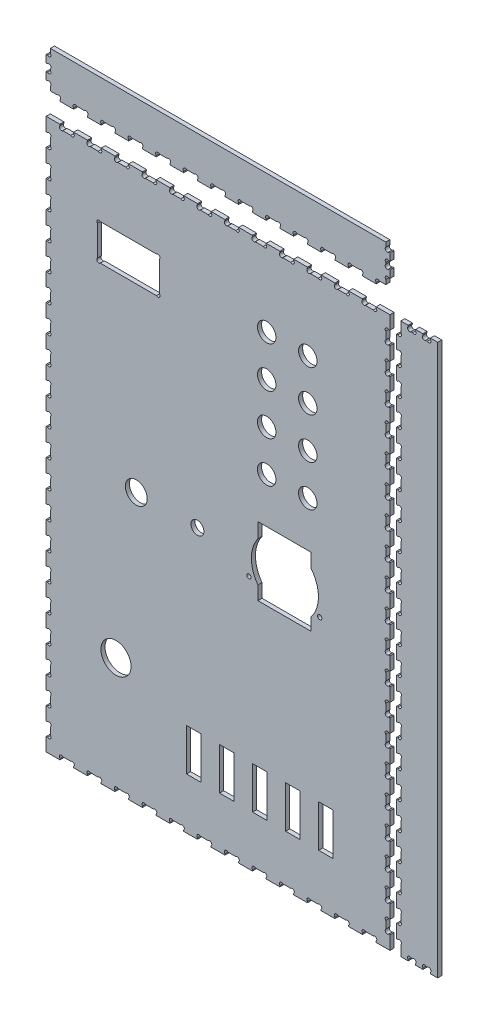
SolidWorks part; units mm, degrees
ref_plane "Alzado" through (0, 0, 0) normal (0, 0, 1) x (1, 0, 0)
ref_plane "Planta" through (0, 0, 0) normal (0, 1, 0) x (1, 0, 0)
ref_plane "Vista lateral" through (0, 0, 0) normal (1, 0, 0) x (0, 0, -1)
sketch "Croquis2" plane through (0, 0, 0) normal (0, 0, 1) x (1, 0, 0)
  line L0 (-12.45, -133) -> (1.075, -133) construction
  line L1 (-125.5, 201) -> (125.5, 201)
  line L2 (-125.5, 201) -> (-125.5, -201)
  line L3 (-125.5, -201) -> (125.5, -201)
  line L4 (125.5, 201) -> (125.5, -201)
  line L5 (-23.05, -163.7) -> (-12.45, -163.7)
  line L6 (-23.05, -163.7) -> (-23.05, -133)
  line L7 (-23.05, -133) -> (-12.45, -133)
  line L8 (-12.45, -163.7) -> (-12.45, -133)
  line L9 (1.075, -163.7) -> (11.675, -163.7)
  line L10 (1.075, -163.7) -> (1.075, -133)
  line L11 (1.075, -133) -> (11.675, -133)
  line L12 (11.675, -163.7) -> (11.675, -133)
  line L13 (25.2, -163.7) -> (35.8, -163.7)
  line L14 (25.2, -163.7) -> (25.2, -133)
  line L15 (25.2, -133) -> (35.8, -133)
  line L16 (35.8, -163.7) -> (35.8, -133)
  line L17 (49.325, -163.7) -> (59.925, -163.7)
  line L18 (49.325, -163.7) -> (49.325, -133)
  line L19 (49.325, -133) -> (59.925, -133)
  line L20 (59.925, -163.7) -> (59.925, -133)
  line L21 (73.45, -163.7) -> (84.05, -163.7)
  line L22 (73.45, -163.7) -> (73.45, -133)
  line L23 (73.45, -133) -> (84.05, -133)
  line L24 (84.05, -163.7) -> (84.05, -133)
  line L25 (11.675, -133) -> (25.2, -133) construction
  line L26 (35.8, -133) -> (49.325, -133) construction
  line L27 (59.925, -133) -> (73.45, -133) construction
  line L28 (22.55, -15.8999) -> (74.25, -15.8999) construction
  line L29 (29.1, 22) -> (67.7, 22)
  line L30 (29.1, 22) -> (29.1, 11.0846)
  line L31 (29.1, -28) -> (67.7, -28)
  line L32 (67.7, 22) -> (67.7, 12.0728)
  line L33 (48.4, -15.8999) -> (48.4, -28) construction
  line L34 (-125.5, -201) -> (125.5, 201) construction
  line L35 (-86.0286, 154.1488) -> (-44.9712, 154.1488)
  line L36 (-42.8499, 152.0275) -> (-42.8499, 129.9701)
  line L37 (-44.9712, 127.8488) -> (-86.0286, 127.8488)
  line L38 (-88.1499, 129.9701) -> (-88.1499, 152.0275)
  line L39 (29.1, 22) -> (67.7, -28) construction
  line L40 (-87.0892, 153.0881) -> (-43.9106, 153.0881) construction
  line L41 (-87.0892, 153.0881) -> (-87.0892, 128.9095) construction
  line L42 (-87.0892, 128.9095) -> (-43.9106, 128.9095) construction
  line L43 (-44.3499, 152.6488) -> (-42.8499, 154.1488) construction
  line L44 (-44.3499, 129.3488) -> (-42.8499, 127.8488) construction
  line L45 (-65.4999, 160.8921) -> (-65.4999, 137.3303) construction
  line L46 (-43.9106, 153.0881) -> (-43.9106, 128.9095) construction
  line L47 (29.1, -18.0846) -> (29.1, -28)
  line L48 (67.7, -19.0728) -> (67.7, -28)
  circle A0 centre (-74.55, -116) radius 11
  circle A1 centre (22.55, -15.8999) radius 1.55
  circle A2 centre (74.25, -15.8999) radius 1.55
  circle A3 centre (-15.0999, -4) radius 4.75
  circle A4 centre (-59.72, -4) radius 8
  arc A5 (-42.8499, 152.0275) -> (-44.9712, 154.1488) centre (-43.9106, 153.0881) ccw
  circle A6 centre (-44.3499, 152.6488) radius 1.5 construction
  arc A7 (-44.9712, 127.8488) -> (-42.8499, 129.9701) centre (-43.9106, 128.9095) ccw
  circle A8 centre (-44.3499, 129.3488) radius 1.5 construction
  arc A9 (-86.0286, 127.8488) -> (-88.1499, 129.9701) centre (-87.0892, 128.9095) cw
  arc A10 (-88.1499, 152.0275) -> (-86.0286, 154.1488) centre (-87.0892, 153.0881) cw
  circle A11 centre (65.5, 145) radius 6.75
  circle A12 centre (35.5, 145) radius 6.75
  circle A13 centre (35.5, 115) radius 6.75
  circle A14 centre (65.5, 115) radius 6.75
  circle A15 centre (35.5, 85) radius 6.75
  circle A16 centre (65.5, 85) radius 6.75
  circle A17 centre (35.5, 55) radius 6.75
  circle A18 centre (65.5, 55) radius 6.75
  arc A19 (29.1, 11.0846) -> (29.1, -18.0846) centre (48.786, -3.5) ccw
  arc A20 (67.7, -19.0728) -> (67.7, 12.0728) centre (48.786, -3.5) ccw
  dimension "D1" = 22
  dimension "D11" = 3.1
  dimension "D18" = 9.5
  dimension "D19" = 16
  dimension "D20" = 65.78
  dimension "D25" = 3
  dimension "D26" = 3
  dimension "D27" = 22.65
  dimension "D21" = 13.5
  dimension "D28" = 60
  dimension "D29" = 56
  dimension "D32" = 205
  dimension "D33" = 110.4001
  dimension "D37" = 49
  dimension "D2" = 402
  dimension "D3" = 251
  dimension "D4" = 10.6
  dimension "D5" = 30.7
  dimension "D6" = 13.525
  dimension "D7" = 41.45
  dimension "D8" = 37.3
  dimension "D9" = 38.6
  dimension "D10" = 50
  dimension "D12" = 51.7
  dimension "D13" = 12.1001
  dimension "D14" = 57.8
  dimension "D15" = 173
  dimension "D16" = 50.95
  dimension "D17" = 85
  dimension "D22" = 30
  dimension "D23" = 37.3501
  dimension "D24" = 46.8512
  dimension "D31" = 30
  dimension "D34" = 26.3
  dimension "D35" = 24.1787
  dimension "D36" = 43.1787
  dimension "D30" = 4
extrude "Saliente-Extruir2" add sketch "Croquis2" along normal blind 3 separate body
sketch "Croquis4" plane through (0, 0, 3) normal (0, 0, 1) x (1, 0, 0)
  line L0 (-125.5, 191.1951) -> (-122.45, 191.1951)
  line L1 (-125.5, 201) -> (-125.5, -201) construction
  line L2 (-122.45, 191.1951) -> (-122.45, 181.3902)
  line L3 (-122.45, 181.3902) -> (-125.5, 181.3902)
  line L4 (-125.5, 191.1951) -> (-125.5, 181.3902)
  line L5 (-125.5, 201) -> (-125.5, 191.1951) construction
  line L6 (-125.5, 181.3902) -> (-125.5, 171.5854) construction
  line L7 (-125.5, 171.5854) -> (-122.45, 171.5854)
  line L8 (-122.45, 171.5854) -> (-122.45, 161.7805)
  line L9 (-122.45, 161.7805) -> (-125.5, 161.7805)
  line L10 (-125.5, 171.5854) -> (-125.5, 161.7805)
  line L11 (-125.5, 161.7805) -> (-125.5, 151.9756) construction
  line L12 (-125.5, 151.9756) -> (-122.45, 151.9756)
  line L13 (-122.45, 151.9756) -> (-122.45, 142.1707)
  line L14 (-122.45, 142.1707) -> (-125.5, 142.1707)
  line L15 (-125.5, 151.9756) -> (-125.5, 142.1707)
  line L16 (-125.5, 142.1707) -> (-125.5, 132.3659) construction
  line L17 (-125.5, 132.3659) -> (-122.45, 132.3659)
  line L18 (-122.45, 132.3659) -> (-122.45, 122.561)
  line L19 (-122.45, 122.561) -> (-125.5, 122.561)
  line L20 (-125.5, 132.3659) -> (-125.5, 122.561)
  line L21 (-125.5, 122.561) -> (-125.5, 112.7561) construction
  line L22 (-125.5, 112.7561) -> (-122.45, 112.7561)
  line L23 (-122.45, 112.7561) -> (-122.45, 102.9512)
  line L24 (-122.45, 102.9512) -> (-125.5, 102.9512)
  line L25 (-125.5, 112.7561) -> (-125.5, 102.9512)
  line L26 (-125.5, 102.9512) -> (-125.5, 93.1463) construction
  line L27 (-125.5, 93.1463) -> (-122.45, 93.1463)
  line L28 (-122.45, 93.1463) -> (-122.45, 83.3415)
  line L29 (-122.45, 83.3415) -> (-125.5, 83.3415)
  line L30 (-125.5, 93.1463) -> (-125.5, 83.3415)
  line L31 (-125.5, 83.3415) -> (-125.5, 73.5366) construction
  line L32 (-125.5, 73.5366) -> (-122.45, 73.5366)
  line L33 (-122.45, 73.5366) -> (-122.45, 63.7317)
  line L34 (-122.45, 63.7317) -> (-125.5, 63.7317)
  line L35 (-125.5, 73.5366) -> (-125.5, 63.7317)
  line L36 (-125.5, 63.7317) -> (-125.5, 53.9268) construction
  line L37 (-125.5, 53.9268) -> (-122.45, 53.9268)
  line L38 (-122.45, 53.9268) -> (-122.45, 44.122)
  line L39 (-122.45, 44.122) -> (-125.5, 44.122)
  line L40 (-125.5, 53.9268) -> (-125.5, 44.122)
  line L41 (-125.5, 44.122) -> (-125.5, 34.3171) construction
  line L42 (-125.5, 34.3171) -> (-122.45, 34.3171)
  line L43 (-122.45, 34.3171) -> (-122.45, 24.5122)
  line L44 (-122.45, 24.5122) -> (-125.5, 24.5122)
  line L45 (-125.5, 34.3171) -> (-125.5, 24.5122)
  line L46 (-125.5, 24.5122) -> (-125.5, 14.7073) construction
  line L47 (-125.5, 14.7073) -> (-122.45, 14.7073)
  line L48 (-122.45, 14.7073) -> (-122.45, 4.9024)
  line L49 (-122.45, 4.9024) -> (-125.5, 4.9024)
  line L50 (-125.5, 14.7073) -> (-125.5, 4.9024)
  line L51 (-125.5, 4.9024) -> (-125.5, -4.9024) construction
  line L52 (-125.5, -4.9024) -> (-122.45, -4.9024)
  line L53 (-122.45, -4.9024) -> (-122.45, -14.7073)
  line L54 (-122.45, -14.7073) -> (-125.5, -14.7073)
  line L55 (-125.5, -4.9024) -> (-125.5, -14.7073)
  line L56 (-125.5, -14.7073) -> (-125.5, -24.5122) construction
  line L57 (-125.5, -24.5122) -> (-122.45, -24.5122)
  line L58 (-122.45, -24.5122) -> (-122.45, -34.3171)
  line L59 (-122.45, -34.3171) -> (-125.5, -34.3171)
  line L60 (-125.5, -24.5122) -> (-125.5, -34.3171)
  line L61 (-125.5, -34.3171) -> (-125.5, -44.122) construction
  line L62 (-125.5, -44.122) -> (-122.45, -44.122)
  line L63 (-122.45, -44.122) -> (-122.45, -53.9268)
  line L64 (-122.45, -53.9268) -> (-125.5, -53.9268)
  line L65 (-125.5, -44.122) -> (-125.5, -53.9268)
  line L66 (-125.5, -53.9268) -> (-125.5, -63.7317) construction
  line L67 (-125.5, -63.7317) -> (-122.45, -63.7317)
  line L68 (-122.45, -63.7317) -> (-122.45, -73.5366)
  line L69 (-122.45, -73.5366) -> (-125.5, -73.5366)
  line L70 (-125.5, -63.7317) -> (-125.5, -73.5366)
  line L71 (-125.5, -73.5366) -> (-125.5, -83.3415) construction
  line L72 (-125.5, -83.3415) -> (-122.45, -83.3415)
  line L73 (-122.45, -83.3415) -> (-122.45, -93.1463)
  line L74 (-122.45, -93.1463) -> (-125.5, -93.1463)
  line L75 (-125.5, -83.3415) -> (-125.5, -93.1463)
  line L76 (-125.5, -93.1463) -> (-125.5, -102.9512) construction
  line L77 (-125.5, -102.9512) -> (-122.45, -102.9512)
  line L78 (-122.45, -102.9512) -> (-122.45, -112.7561)
  line L79 (-122.45, -112.7561) -> (-125.5, -112.7561)
  line L80 (-125.5, -102.9512) -> (-125.5, -112.7561)
  line L81 (-125.5, -112.7561) -> (-125.5, -122.561) construction
  line L82 (-125.5, -122.561) -> (-122.45, -122.561)
  line L83 (-122.45, -122.561) -> (-122.45, -132.3659)
  line L84 (-122.45, -132.3659) -> (-125.5, -132.3659)
  line L85 (-125.5, -122.561) -> (-125.5, -132.3659)
  line L86 (-125.5, -132.3659) -> (-125.5, -142.1707) construction
  line L87 (-125.5, -142.1707) -> (-122.45, -142.1707)
  line L88 (-122.45, -142.1707) -> (-122.45, -151.9756)
  line L89 (-122.45, -151.9756) -> (-125.5, -151.9756)
  line L90 (-125.5, -142.1707) -> (-125.5, -151.9756)
  line L91 (-125.5, -151.9756) -> (-125.5, -161.7805) construction
  line L92 (-125.5, -161.7805) -> (-122.45, -161.7805)
  line L93 (-122.45, -161.7805) -> (-122.45, -171.5854)
  line L94 (-122.45, -171.5854) -> (-125.5, -171.5854)
  line L95 (-125.5, -161.7805) -> (-125.5, -171.5854)
  line L96 (-125.5, -171.5854) -> (-125.5, -181.3902) construction
  line L97 (-125.5, -181.3902) -> (-122.45, -181.3902)
  line L98 (-122.45, -181.3902) -> (-122.45, -191.1951)
  line L99 (-122.45, -191.1951) -> (-125.5, -191.1951)
  line L100 (-125.5, -181.3902) -> (-125.5, -191.1951)
  line L101 (-125.5, -191.1951) -> (-125.5, -201) construction
  line L102 (0, 201) -> (0, 0) construction
  line L103 (125.5, 201) -> (-125.5, 201) construction
  line L104 (125.5, -191.1951) -> (125.5, -201) construction
  line L105 (125.5, -171.5854) -> (125.5, -181.3902) construction
  line L106 (125.5, -151.9756) -> (125.5, -161.7805) construction
  line L107 (125.5, -132.3659) -> (125.5, -142.1707) construction
  line L108 (125.5, -112.7561) -> (125.5, -122.561) construction
  line L109 (125.5, -93.1463) -> (125.5, -102.9512) construction
  line L110 (125.5, -73.5366) -> (125.5, -83.3415) construction
  line L111 (125.5, -53.9268) -> (125.5, -63.7317) construction
  line L112 (125.5, -34.3171) -> (125.5, -44.122) construction
  line L113 (125.5, -14.7073) -> (125.5, -24.5122) construction
  line L114 (125.5, 4.9024) -> (125.5, -4.9024) construction
  line L115 (125.5, 24.5122) -> (125.5, 14.7073) construction
  line L116 (125.5, 44.122) -> (125.5, 34.3171) construction
  line L117 (125.5, 63.7317) -> (125.5, 53.9268) construction
  line L118 (125.5, 83.3415) -> (125.5, 73.5366) construction
  line L119 (125.5, 102.9512) -> (125.5, 93.1463) construction
  line L120 (125.5, 122.561) -> (125.5, 112.7561) construction
  line L121 (125.5, 142.1707) -> (125.5, 132.3659) construction
  line L122 (125.5, 161.7805) -> (125.5, 151.9756) construction
  line L123 (125.5, 181.3902) -> (125.5, 171.5854) construction
  line L124 (125.5, 201) -> (125.5, 191.1951) construction
  line L125 (125.5, -181.3902) -> (125.5, -191.1951)
  line L126 (122.45, -191.1951) -> (125.5, -191.1951)
  line L127 (122.45, -181.3902) -> (122.45, -191.1951)
  line L128 (125.5, -181.3902) -> (122.45, -181.3902)
  line L129 (125.5, -161.7805) -> (125.5, -171.5854)
  line L130 (122.45, -171.5854) -> (125.5, -171.5854)
  line L131 (122.45, -161.7805) -> (122.45, -171.5854)
  line L132 (125.5, -161.7805) -> (122.45, -161.7805)
  line L133 (125.5, -142.1707) -> (125.5, -151.9756)
  line L134 (122.45, -151.9756) -> (125.5, -151.9756)
  line L135 (122.45, -142.1707) -> (122.45, -151.9756)
  line L136 (125.5, -142.1707) -> (122.45, -142.1707)
  line L137 (125.5, -122.561) -> (125.5, -132.3659)
  line L138 (122.45, -132.3659) -> (125.5, -132.3659)
  line L139 (122.45, -122.561) -> (122.45, -132.3659)
  line L140 (125.5, -122.561) -> (122.45, -122.561)
  line L141 (125.5, -102.9512) -> (125.5, -112.7561)
  line L142 (122.45, -112.7561) -> (125.5, -112.7561)
  line L143 (122.45, -102.9512) -> (122.45, -112.7561)
  line L144 (125.5, -102.9512) -> (122.45, -102.9512)
  line L145 (125.5, -83.3415) -> (125.5, -93.1463)
  line L146 (122.45, -93.1463) -> (125.5, -93.1463)
  line L147 (122.45, -83.3415) -> (122.45, -93.1463)
  line L148 (125.5, -83.3415) -> (122.45, -83.3415)
  line L149 (125.5, -63.7317) -> (125.5, -73.5366)
  line L150 (122.45, -73.5366) -> (125.5, -73.5366)
  line L151 (122.45, -63.7317) -> (122.45, -73.5366)
  line L152 (125.5, -63.7317) -> (122.45, -63.7317)
  line L153 (125.5, -44.122) -> (125.5, -53.9268)
  line L154 (122.45, -53.9268) -> (125.5, -53.9268)
  line L155 (122.45, -44.122) -> (122.45, -53.9268)
  line L156 (125.5, -44.122) -> (122.45, -44.122)
  line L157 (125.5, -24.5122) -> (125.5, -34.3171)
  line L158 (122.45, -34.3171) -> (125.5, -34.3171)
  line L159 (122.45, -24.5122) -> (122.45, -34.3171)
  line L160 (125.5, -24.5122) -> (122.45, -24.5122)
  line L161 (125.5, -4.9024) -> (125.5, -14.7073)
  line L162 (122.45, -14.7073) -> (125.5, -14.7073)
  line L163 (122.45, -4.9024) -> (122.45, -14.7073)
  line L164 (125.5, -4.9024) -> (122.45, -4.9024)
  line L165 (125.5, 14.7073) -> (125.5, 4.9024)
  line L166 (122.45, 4.9024) -> (125.5, 4.9024)
  line L167 (122.45, 14.7073) -> (122.45, 4.9024)
  line L168 (125.5, 14.7073) -> (122.45, 14.7073)
  line L169 (125.5, 34.3171) -> (125.5, 24.5122)
  line L170 (122.45, 24.5122) -> (125.5, 24.5122)
  line L171 (122.45, 34.3171) -> (122.45, 24.5122)
  line L172 (125.5, 34.3171) -> (122.45, 34.3171)
  line L173 (125.5, 53.9268) -> (125.5, 44.122)
  line L174 (122.45, 44.122) -> (125.5, 44.122)
  line L175 (122.45, 53.9268) -> (122.45, 44.122)
  line L176 (125.5, 53.9268) -> (122.45, 53.9268)
  line L177 (125.5, 73.5366) -> (125.5, 63.7317)
  line L178 (122.45, 63.7317) -> (125.5, 63.7317)
  line L179 (122.45, 73.5366) -> (122.45, 63.7317)
  line L180 (125.5, 73.5366) -> (122.45, 73.5366)
  line L181 (125.5, 93.1463) -> (125.5, 83.3415)
  line L182 (122.45, 83.3415) -> (125.5, 83.3415)
  line L183 (122.45, 93.1463) -> (122.45, 83.3415)
  line L184 (125.5, 93.1463) -> (122.45, 93.1463)
  line L185 (125.5, 112.7561) -> (125.5, 102.9512)
  line L186 (122.45, 102.9512) -> (125.5, 102.9512)
  line L187 (122.45, 112.7561) -> (122.45, 102.9512)
  line L188 (125.5, 112.7561) -> (122.45, 112.7561)
  line L189 (125.5, 132.3659) -> (125.5, 122.561)
  line L190 (122.45, 122.561) -> (125.5, 122.561)
  line L191 (122.45, 132.3659) -> (122.45, 122.561)
  line L192 (125.5, 132.3659) -> (122.45, 132.3659)
  line L193 (125.5, 151.9756) -> (125.5, 142.1707)
  line L194 (122.45, 142.1707) -> (125.5, 142.1707)
  line L195 (122.45, 151.9756) -> (122.45, 142.1707)
  line L196 (125.5, 151.9756) -> (122.45, 151.9756)
  line L197 (125.5, 171.5854) -> (125.5, 161.7805)
  line L198 (122.45, 161.7805) -> (125.5, 161.7805)
  line L199 (122.45, 171.5854) -> (122.45, 161.7805)
  line L200 (125.5, 171.5854) -> (122.45, 171.5854)
  line L201 (125.5, 191.1951) -> (125.5, 181.3902)
  line L202 (122.45, 181.3902) -> (125.5, 181.3902)
  line L203 (122.45, 191.1951) -> (122.45, 181.3902)
  line L204 (125.5, 191.1951) -> (122.45, 191.1951)
  dimension "D1" = 3.05
  dimension "D2" = 20
extrude "Cortar-Extruir1" cut sketch "Croquis4" against normal through all
sketch "Croquis5" plane through (0, 0, 3) normal (0, 0, 1) x (1, 0, 0)
  line L0 (125.5, 201) -> (-125.5, 201) construction
  line L1 (-115.46, 201) -> (-105.42, 201)
  line L2 (-115.46, 201) -> (-115.46, 197.95)
  line L3 (-115.46, 197.95) -> (-105.42, 197.95)
  line L4 (-105.42, 201) -> (-105.42, 197.95)
  line L5 (-115.46, 201) -> (-125.5, 201) construction
  line L6 (-122.45, 191.1951) -> (-125.5, 191.1951) construction
  line L7 (-95.38, 201) -> (-85.34, 201)
  line L8 (-95.38, 201) -> (-95.38, 197.95)
  line L9 (-95.38, 197.95) -> (-85.34, 197.95)
  line L10 (-85.34, 201) -> (-85.34, 197.95)
  line L11 (-95.38, 201) -> (-105.42, 201) construction
  line L12 (-75.3, 201) -> (-65.26, 201)
  line L13 (-75.3, 201) -> (-75.3, 197.95)
  line L14 (-75.3, 197.95) -> (-65.26, 197.95)
  line L15 (-65.26, 201) -> (-65.26, 197.95)
  line L16 (-75.3, 201) -> (-85.34, 201) construction
  line L17 (-55.22, 201) -> (-45.18, 201)
  line L18 (-55.22, 201) -> (-55.22, 197.95)
  line L19 (-55.22, 197.95) -> (-45.18, 197.95)
  line L20 (-45.18, 201) -> (-45.18, 197.95)
  line L21 (-55.22, 201) -> (-65.26, 201) construction
  line L22 (-35.14, 201) -> (-25.1, 201)
  line L23 (-35.14, 201) -> (-35.14, 197.95)
  line L24 (-35.14, 197.95) -> (-25.1, 197.95)
  line L25 (-25.1, 201) -> (-25.1, 197.95)
  line L26 (-35.14, 201) -> (-45.18, 201) construction
  line L27 (-15.06, 201) -> (-5.02, 201)
  line L28 (-15.06, 201) -> (-15.06, 197.95)
  line L29 (-15.06, 197.95) -> (-5.02, 197.95)
  line L30 (-5.02, 201) -> (-5.02, 197.95)
  line L31 (-15.06, 201) -> (-25.1, 201) construction
  line L32 (5.02, 201) -> (15.06, 201)
  line L33 (5.02, 201) -> (5.02, 197.95)
  line L34 (5.02, 197.95) -> (15.06, 197.95)
  line L35 (15.06, 201) -> (15.06, 197.95)
  line L36 (5.02, 201) -> (-5.02, 201) construction
  line L37 (25.1, 201) -> (35.14, 201)
  line L38 (25.1, 201) -> (25.1, 197.95)
  line L39 (25.1, 197.95) -> (35.14, 197.95)
  line L40 (35.14, 201) -> (35.14, 197.95)
  line L41 (25.1, 201) -> (15.06, 201) construction
  line L42 (45.18, 201) -> (55.22, 201)
  line L43 (45.18, 201) -> (45.18, 197.95)
  line L44 (45.18, 197.95) -> (55.22, 197.95)
  line L45 (55.22, 201) -> (55.22, 197.95)
  line L46 (45.18, 201) -> (35.14, 201) construction
  line L47 (65.26, 201) -> (75.3, 201)
  line L48 (65.26, 201) -> (65.26, 197.95)
  line L49 (65.26, 197.95) -> (75.3, 197.95)
  line L50 (75.3, 201) -> (75.3, 197.95)
  line L51 (65.26, 201) -> (55.22, 201) construction
  line L52 (85.34, 201) -> (95.38, 201)
  line L53 (85.34, 201) -> (85.34, 197.95)
  line L54 (85.34, 197.95) -> (95.38, 197.95)
  line L55 (95.38, 201) -> (95.38, 197.95)
  line L56 (85.34, 201) -> (75.3, 201) construction
  line L57 (105.42, 201) -> (115.46, 201)
  line L58 (105.42, 201) -> (105.42, 197.95)
  line L59 (105.42, 197.95) -> (115.46, 197.95)
  line L60 (115.46, 201) -> (115.46, 197.95)
  line L61 (105.42, 201) -> (95.38, 201) construction
  line L62 (115.46, 201) -> (125.5, 201) construction
  line L63 (0, 0) -> (108.8157, 0) construction
  line L64 (115.46, -201) -> (125.5, -201) construction
  line L65 (105.42, -201) -> (95.38, -201) construction
  line L66 (85.34, -201) -> (75.3, -201) construction
  line L67 (65.26, -201) -> (55.22, -201) construction
  line L68 (45.18, -201) -> (35.14, -201) construction
  line L69 (25.1, -201) -> (15.06, -201) construction
  line L70 (5.02, -201) -> (-5.02, -201) construction
  line L71 (-15.06, -201) -> (-25.1, -201) construction
  line L72 (-35.14, -201) -> (-45.18, -201) construction
  line L73 (-55.22, -201) -> (-65.26, -201) construction
  line L74 (-75.3, -201) -> (-85.34, -201) construction
  line L75 (-95.38, -201) -> (-105.42, -201) construction
  line L76 (-115.46, -201) -> (-125.5, -201) construction
  line L77 (115.46, -201) -> (115.46, -197.95)
  line L78 (105.42, -197.95) -> (115.46, -197.95)
  line L79 (105.42, -201) -> (105.42, -197.95)
  line L80 (105.42, -201) -> (115.46, -201)
  line L81 (95.38, -201) -> (95.38, -197.95)
  line L82 (85.34, -197.95) -> (95.38, -197.95)
  line L83 (85.34, -201) -> (85.34, -197.95)
  line L84 (85.34, -201) -> (95.38, -201)
  line L85 (75.3, -201) -> (75.3, -197.95)
  line L86 (65.26, -197.95) -> (75.3, -197.95)
  line L87 (65.26, -201) -> (65.26, -197.95)
  line L88 (65.26, -201) -> (75.3, -201)
  line L89 (55.22, -201) -> (55.22, -197.95)
  line L90 (45.18, -197.95) -> (55.22, -197.95)
  line L91 (45.18, -201) -> (45.18, -197.95)
  line L92 (45.18, -201) -> (55.22, -201)
  line L93 (35.14, -201) -> (35.14, -197.95)
  line L94 (25.1, -197.95) -> (35.14, -197.95)
  line L95 (25.1, -201) -> (25.1, -197.95)
  line L96 (25.1, -201) -> (35.14, -201)
  line L97 (15.06, -201) -> (15.06, -197.95)
  line L98 (5.02, -197.95) -> (15.06, -197.95)
  line L99 (5.02, -201) -> (5.02, -197.95)
  line L100 (5.02, -201) -> (15.06, -201)
  line L101 (-5.02, -201) -> (-5.02, -197.95)
  line L102 (-15.06, -197.95) -> (-5.02, -197.95)
  line L103 (-15.06, -201) -> (-15.06, -197.95)
  line L104 (-15.06, -201) -> (-5.02, -201)
  line L105 (-25.1, -201) -> (-25.1, -197.95)
  line L106 (-35.14, -197.95) -> (-25.1, -197.95)
  line L107 (-35.14, -201) -> (-35.14, -197.95)
  line L108 (-35.14, -201) -> (-25.1, -201)
  line L109 (-45.18, -201) -> (-45.18, -197.95)
  line L110 (-55.22, -197.95) -> (-45.18, -197.95)
  line L111 (-55.22, -201) -> (-55.22, -197.95)
  line L112 (-55.22, -201) -> (-45.18, -201)
  line L113 (-65.26, -201) -> (-65.26, -197.95)
  line L114 (-75.3, -197.95) -> (-65.26, -197.95)
  line L115 (-75.3, -201) -> (-75.3, -197.95)
  line L116 (-75.3, -201) -> (-65.26, -201)
  line L117 (-85.34, -201) -> (-85.34, -197.95)
  line L118 (-95.38, -197.95) -> (-85.34, -197.95)
  line L119 (-95.38, -201) -> (-95.38, -197.95)
  line L120 (-95.38, -201) -> (-85.34, -201)
  line L121 (-105.42, -201) -> (-105.42, -197.95)
  line L122 (-115.46, -197.95) -> (-105.42, -197.95)
  line L123 (-115.46, -201) -> (-115.46, -197.95)
  line L124 (-115.46, -201) -> (-105.42, -201)
  dimension "D1" = 12
extrude "Cortar-Extruir2" cut sketch "Croquis5" against normal through all
sketch "Croquis12" plane through (0, 0, 0) normal (0, 0, 1) x (1, 0, 0)
  line L1 (130.3668, 201) -> (160.3668, 201)
  line L2 (130.3668, 201) -> (130.3668, -201)
  line L3 (130.3668, -201) -> (160.3668, -201)
  line L4 (160.3668, 201) -> (160.3668, -201)
  line L5 (-125.5, 245.4596) -> (125.5, 245.4596)
  line L6 (-125.5, 245.4596) -> (-125.5, 215.4596)
  line L7 (-125.5, 215.4596) -> (125.5, 215.4596)
  line L8 (125.5, 245.4596) -> (125.5, 215.4596)
  line L13 (-125.5, 201) -> (-125.5, 191.1951) construction
  dimension "D1" = 402
  dimension "D2" = 30
  dimension "D3" = 251
extrude "Saliente-Extruir3" add sketch "Croquis12" along normal blind 3 separate body
sketch "Croquis13" plane through (0, 0, 3) normal (0, 0, 1) x (1, 0, 0)
  line L0 (130.3668, 201) -> (130.3668, -201) construction
  line L1 (130.3668, 201) -> (133.4168, 201)
  line L2 (130.3668, 201) -> (130.3668, 191.1951)
  line L3 (130.3668, 191.1951) -> (133.4168, 191.1951)
  line L4 (133.4168, 201) -> (133.4168, 191.1951)
  line L5 (160.3668, 201) -> (130.3668, 201) construction
  line L6 (125.5, 191.1951) -> (122.45, 191.1951) construction
  line L7 (130.3668, 191.1951) -> (130.3668, 181.3902) construction
  line L11 (130.3668, 181.3902) -> (133.4168, 181.3902)
  line L12 (130.3668, 181.3902) -> (130.3668, 171.5854)
  line L13 (130.3668, 171.5854) -> (133.4168, 171.5854)
  line L14 (133.4168, 181.3902) -> (133.4168, 171.5854)
  line L16 (130.3668, 161.7805) -> (133.4168, 161.7805)
  line L17 (130.3668, 161.7805) -> (130.3668, 151.9756)
  line L18 (130.3668, 151.9756) -> (133.4168, 151.9756)
  line L19 (133.4168, 161.7805) -> (133.4168, 151.9756)
  line L20 (130.3668, 171.5854) -> (130.3668, 161.7805) construction
  line L21 (130.3668, 142.1707) -> (133.4168, 142.1707)
  line L22 (130.3668, 142.1707) -> (130.3668, 132.3659)
  line L23 (130.3668, 132.3659) -> (133.4168, 132.3659)
  line L24 (133.4168, 142.1707) -> (133.4168, 132.3659)
  line L25 (130.3668, 151.9756) -> (130.3668, 142.1707) construction
  line L26 (130.3668, 122.561) -> (133.4168, 122.561)
  line L27 (130.3668, 122.561) -> (130.3668, 112.7561)
  line L28 (130.3668, 112.7561) -> (133.4168, 112.7561)
  line L29 (133.4168, 122.561) -> (133.4168, 112.7561)
  line L30 (130.3668, 132.3659) -> (130.3668, 122.561) construction
  line L31 (130.3668, 102.9512) -> (133.4168, 102.9512)
  line L32 (130.3668, 102.9512) -> (130.3668, 93.1463)
  line L33 (130.3668, 93.1463) -> (133.4168, 93.1463)
  line L34 (133.4168, 102.9512) -> (133.4168, 93.1463)
  line L35 (130.3668, 112.7561) -> (130.3668, 102.9512) construction
  line L36 (130.3668, 83.3415) -> (133.4168, 83.3415)
  line L37 (130.3668, 83.3415) -> (130.3668, 73.5366)
  line L38 (130.3668, 73.5366) -> (133.4168, 73.5366)
  line L39 (133.4168, 83.3415) -> (133.4168, 73.5366)
  line L40 (130.3668, 93.1463) -> (130.3668, 83.3415) construction
  line L41 (130.3668, 63.7317) -> (133.4168, 63.7317)
  line L42 (130.3668, 63.7317) -> (130.3668, 53.9268)
  line L43 (130.3668, 53.9268) -> (133.4168, 53.9268)
  line L44 (133.4168, 63.7317) -> (133.4168, 53.9268)
  line L45 (130.3668, 73.5366) -> (130.3668, 63.7317) construction
  line L46 (130.3668, 44.122) -> (133.4168, 44.122)
  line L47 (130.3668, 44.122) -> (130.3668, 34.3171)
  line L48 (130.3668, 34.3171) -> (133.4168, 34.3171)
  line L49 (133.4168, 44.122) -> (133.4168, 34.3171)
  line L50 (130.3668, 53.9268) -> (130.3668, 44.122) construction
  line L51 (130.3668, 24.5122) -> (133.4168, 24.5122)
  line L52 (130.3668, 24.5122) -> (130.3668, 14.7073)
  line L53 (130.3668, 14.7073) -> (133.4168, 14.7073)
  line L54 (133.4168, 24.5122) -> (133.4168, 14.7073)
  line L55 (130.3668, 34.3171) -> (130.3668, 24.5122) construction
  line L56 (130.3668, 4.9024) -> (133.4168, 4.9024)
  line L57 (130.3668, 4.9024) -> (130.3668, -4.9024)
  line L58 (130.3668, -4.9024) -> (133.4168, -4.9024)
  line L59 (133.4168, 4.9024) -> (133.4168, -4.9024)
  line L60 (130.3668, 14.7073) -> (130.3668, 4.9024) construction
  line L61 (130.3668, -14.7073) -> (133.4168, -14.7073)
  line L62 (130.3668, -14.7073) -> (130.3668, -24.5122)
  line L63 (130.3668, -24.5122) -> (133.4168, -24.5122)
  line L64 (133.4168, -14.7073) -> (133.4168, -24.5122)
  line L65 (130.3668, -4.9024) -> (130.3668, -14.7073) construction
  line L66 (130.3668, -34.3171) -> (133.4168, -34.3171)
  line L67 (130.3668, -34.3171) -> (130.3668, -44.122)
  line L68 (130.3668, -44.122) -> (133.4168, -44.122)
  line L69 (133.4168, -34.3171) -> (133.4168, -44.122)
  line L70 (130.3668, -24.5122) -> (130.3668, -34.3171) construction
  line L71 (130.3668, -53.9268) -> (133.4168, -53.9268)
  line L72 (130.3668, -53.9268) -> (130.3668, -63.7317)
  line L73 (130.3668, -63.7317) -> (133.4168, -63.7317)
  line L74 (133.4168, -53.9268) -> (133.4168, -63.7317)
  line L75 (130.3668, -44.122) -> (130.3668, -53.9268) construction
  line L76 (130.3668, -73.5366) -> (133.4168, -73.5366)
  line L77 (130.3668, -73.5366) -> (130.3668, -83.3415)
  line L78 (130.3668, -83.3415) -> (133.4168, -83.3415)
  line L79 (133.4168, -73.5366) -> (133.4168, -83.3415)
  line L80 (130.3668, -63.7317) -> (130.3668, -73.5366) construction
  line L81 (130.3668, -93.1463) -> (133.4168, -93.1463)
  line L82 (130.3668, -93.1463) -> (130.3668, -102.9512)
  line L83 (130.3668, -102.9512) -> (133.4168, -102.9512)
  line L84 (133.4168, -93.1463) -> (133.4168, -102.9512)
  line L85 (130.3668, -83.3415) -> (130.3668, -93.1463) construction
  line L86 (130.3668, -112.7561) -> (133.4168, -112.7561)
  line L87 (130.3668, -112.7561) -> (130.3668, -122.561)
  line L88 (130.3668, -122.561) -> (133.4168, -122.561)
  line L89 (133.4168, -112.7561) -> (133.4168, -122.561)
  line L90 (130.3668, -102.9512) -> (130.3668, -112.7561) construction
  line L91 (130.3668, -132.3659) -> (133.4168, -132.3659)
  line L92 (130.3668, -132.3659) -> (130.3668, -142.1707)
  line L93 (130.3668, -142.1707) -> (133.4168, -142.1707)
  line L94 (133.4168, -132.3659) -> (133.4168, -142.1707)
  line L95 (130.3668, -122.561) -> (130.3668, -132.3659) construction
  line L96 (130.3668, -151.9756) -> (133.4168, -151.9756)
  line L97 (130.3668, -151.9756) -> (130.3668, -161.7805)
  line L98 (130.3668, -161.7805) -> (133.4168, -161.7805)
  line L99 (133.4168, -151.9756) -> (133.4168, -161.7805)
  line L100 (130.3668, -142.1707) -> (130.3668, -151.9756) construction
  line L101 (130.3668, -171.5854) -> (133.4168, -171.5854)
  line L102 (130.3668, -171.5854) -> (130.3668, -181.3902)
  line L103 (130.3668, -181.3902) -> (133.4168, -181.3902)
  line L104 (133.4168, -171.5854) -> (133.4168, -181.3902)
  line L105 (130.3668, -161.7805) -> (130.3668, -171.5854) construction
  line L107 (130.3668, -201) -> (133.4168, -201)
  line L108 (130.3668, -201) -> (130.3668, -191.1951)
  line L109 (130.3668, -191.1951) -> (133.4168, -191.1951)
  line L110 (133.4168, -201) -> (133.4168, -191.1951)
  line L111 (122.45, 181.3902) -> (125.5, 181.3902) construction
  line L112 (125.5, 171.5854) -> (122.45, 171.5854) construction
  line L113 (122.45, -191.1951) -> (125.5, -191.1951) construction
  dimension "D4" = 19
extrude "Cortar-Extruir8" cut sketch "Croquis13" against normal through all
sketch "Croquis14" plane through (0, 0, 3) normal (0, 0, 1) x (1, 0, 0)
  line L0 (160.3668, 201) -> (133.4168, 201) construction
  line L1 (138.8068, 201) -> (144.1968, 201)
  line L2 (138.8068, 201) -> (138.8068, 197.95)
  line L3 (138.8068, 197.95) -> (144.1968, 197.95)
  line L4 (144.1968, 201) -> (144.1968, 197.95)
  line L5 (130.3668, 191.1951) -> (133.4168, 191.1951) construction
  line L6 (149.5868, 201) -> (154.9768, 201)
  line L7 (149.5868, 201) -> (149.5868, 197.95)
  line L8 (149.5868, 197.95) -> (154.9768, 197.95)
  line L9 (154.9768, 201) -> (154.9768, 197.95)
  line L10 (144.1968, 201) -> (149.5868, 201) construction
  line L11 (154.9768, 201) -> (160.3668, 201) construction
  line L12 (133.4168, 201) -> (138.8068, 201) construction
  line L13 (160.3668, 0) -> (144.1968, 0) construction
  line L14 (160.3668, -201) -> (160.3668, 201) construction
  line L15 (133.4168, -201) -> (138.8068, -201) construction
  line L16 (154.9768, -201) -> (160.3668, -201) construction
  line L17 (144.1968, -201) -> (149.5868, -201) construction
  line L18 (154.9768, -201) -> (154.9768, -197.95)
  line L19 (149.5868, -197.95) -> (154.9768, -197.95)
  line L20 (149.5868, -201) -> (149.5868, -197.95)
  line L21 (149.5868, -201) -> (154.9768, -201)
  line L22 (144.1968, -201) -> (144.1968, -197.95)
  line L23 (138.8068, -197.95) -> (144.1968, -197.95)
  line L24 (138.8068, -201) -> (138.8068, -197.95)
  line L25 (138.8068, -201) -> (144.1968, -201)
extrude "Cortar-Extruir9" cut sketch "Croquis14" against normal through all
sketch "Croquis16" plane through (0, 0, 3) normal (0, 0, 1) x (1, 0, 0)
  line L0 (-105.42, 197.95) -> (-105.42, 201) construction
  line L1 (-125.5, 215.4596) -> (125.5, 215.4596) construction
  line L2 (-125.5, 215.4596) -> (-115.46, 215.4596)
  line L3 (-125.5, 215.4596) -> (-125.5, 218.5096)
  line L4 (-125.5, 218.5096) -> (-115.46, 218.5096)
  line L5 (-115.46, 215.4596) -> (-115.46, 218.5096)
  line L6 (-95.38, 201) -> (-95.38, 197.95) construction
  line L10 (-115.46, 201) -> (-115.46, 197.95) construction
  line L12 (-125.5, 245.4596) -> (-125.5, 215.4596) construction
  line L13 (-115.46, 215.4596) -> (-105.42, 215.4596) construction
  line L14 (-105.42, 215.4596) -> (-95.38, 215.4596)
  line L15 (-105.42, 215.4596) -> (-105.42, 218.5096)
  line L16 (-105.42, 218.5096) -> (-95.38, 218.5096)
  line L17 (-95.38, 215.4596) -> (-95.38, 218.5096)
  line L20 (-85.34, 215.4596) -> (-75.3, 215.4596)
  line L21 (-85.34, 215.4596) -> (-85.34, 218.5096)
  line L22 (-85.34, 218.5096) -> (-75.3, 218.5096)
  line L23 (-75.3, 215.4596) -> (-75.3, 218.5096)
  line L24 (-95.38, 215.4596) -> (-85.34, 215.4596) construction
  line L25 (-65.26, 215.4596) -> (-55.22, 215.4596)
  line L26 (-65.26, 215.4596) -> (-65.26, 218.5096)
  line L27 (-65.26, 218.5096) -> (-55.22, 218.5096)
  line L28 (-55.22, 215.4596) -> (-55.22, 218.5096)
  line L29 (-75.3, 215.4596) -> (-65.26, 215.4596) construction
  line L30 (-45.18, 215.4596) -> (-35.14, 215.4596)
  line L31 (-45.18, 215.4596) -> (-45.18, 218.5096)
  line L32 (-45.18, 218.5096) -> (-35.14, 218.5096)
  line L33 (-35.14, 215.4596) -> (-35.14, 218.5096)
  line L34 (-55.22, 215.4596) -> (-45.18, 215.4596) construction
  line L35 (-25.1, 215.4596) -> (-15.06, 215.4596)
  line L36 (-25.1, 215.4596) -> (-25.1, 218.5096)
  line L37 (-25.1, 218.5096) -> (-15.06, 218.5096)
  line L38 (-15.06, 215.4596) -> (-15.06, 218.5096)
  line L39 (-35.14, 215.4596) -> (-25.1, 215.4596) construction
  line L40 (-5.02, 215.4596) -> (5.02, 215.4596)
  line L41 (-5.02, 215.4596) -> (-5.02, 218.5096)
  line L42 (-5.02, 218.5096) -> (5.02, 218.5096)
  line L43 (5.02, 215.4596) -> (5.02, 218.5096)
  line L44 (-15.06, 215.4596) -> (-5.02, 215.4596) construction
  line L45 (15.06, 215.4596) -> (25.1, 215.4596)
  line L46 (15.06, 215.4596) -> (15.06, 218.5096)
  line L47 (15.06, 218.5096) -> (25.1, 218.5096)
  line L48 (25.1, 215.4596) -> (25.1, 218.5096)
  line L49 (5.02, 215.4596) -> (15.06, 215.4596) construction
  line L50 (35.14, 215.4596) -> (45.18, 215.4596)
  line L51 (35.14, 215.4596) -> (35.14, 218.5096)
  line L52 (35.14, 218.5096) -> (45.18, 218.5096)
  line L53 (45.18, 215.4596) -> (45.18, 218.5096)
  line L54 (25.1, 215.4596) -> (35.14, 215.4596) construction
  line L55 (55.22, 215.4596) -> (65.26, 215.4596)
  line L56 (55.22, 215.4596) -> (55.22, 218.5096)
  line L57 (55.22, 218.5096) -> (65.26, 218.5096)
  line L58 (65.26, 215.4596) -> (65.26, 218.5096)
  line L59 (45.18, 215.4596) -> (55.22, 215.4596) construction
  line L60 (75.3, 215.4596) -> (85.34, 215.4596)
  line L61 (75.3, 215.4596) -> (75.3, 218.5096)
  line L62 (75.3, 218.5096) -> (85.34, 218.5096)
  line L63 (85.34, 215.4596) -> (85.34, 218.5096)
  line L64 (65.26, 215.4596) -> (75.3, 215.4596) construction
  line L65 (95.38, 215.4596) -> (105.42, 215.4596)
  line L66 (95.38, 215.4596) -> (95.38, 218.5096)
  line L67 (95.38, 218.5096) -> (105.42, 218.5096)
  line L68 (105.42, 215.4596) -> (105.42, 218.5096)
  line L69 (85.34, 215.4596) -> (95.38, 215.4596) construction
  line L70 (115.46, 215.4596) -> (125.5, 215.4596)
  line L71 (115.46, 215.4596) -> (115.46, 218.5096)
  line L72 (115.46, 218.5096) -> (125.5, 218.5096)
  line L73 (125.5, 215.4596) -> (125.5, 218.5096)
  line L74 (105.42, 215.4596) -> (115.46, 215.4596) construction
  dimension "D4" = 12
extrude "Cortar-Extruir10" cut sketch "Croquis16" against normal through all
sketch "Croquis18" plane through (0, 0, 3) normal (0, 0, 1) x (1, 0, 0)
  line L0 (0, 245.4596) -> (0, 229.0396) construction
  line L1 (138.8068, 201) -> (138.8068, 197.95) construction
  line L2 (125.5, 218.5096) -> (122.45, 218.5096)
  line L3 (125.5, 218.5096) -> (125.5, 223.8996)
  line L4 (125.5, 223.8996) -> (122.45, 223.8996)
  line L5 (125.5, 245.4596) -> (-125.5, 245.4596) construction
  line L6 (122.45, 218.5096) -> (122.45, 223.8996)
  line L7 (125.5, 245.4596) -> (122.45, 245.4596)
  line L8 (125.5, 245.4596) -> (125.5, 240.0696)
  line L9 (125.5, 240.0696) -> (122.45, 240.0696)
  line L10 (-125.5, 229.2896) -> (-125.5, 223.8996) construction
  line L11 (122.45, 245.4596) -> (122.45, 240.0696)
  line L12 (125.5, 218.5096) -> (125.5, 245.4596) construction
  line L13 (125.5, 234.6796) -> (122.45, 234.6796)
  line L14 (125.5, 234.6796) -> (125.5, 229.2896)
  line L15 (125.5, 229.2896) -> (122.45, 229.2896)
  line L16 (122.45, 234.6796) -> (122.45, 229.2896)
  line L17 (125.5, 240.0696) -> (125.5, 234.6796) construction
  line L18 (125.5, 229.2896) -> (125.5, 223.8996) construction
  line L19 (-125.5, 240.0696) -> (-125.5, 234.6796) construction
  line L20 (-122.45, 234.6796) -> (-122.45, 229.2896)
  line L21 (-125.5, 229.2896) -> (-122.45, 229.2896)
  line L22 (-125.5, 234.6796) -> (-125.5, 229.2896)
  line L23 (-125.5, 234.6796) -> (-122.45, 234.6796)
  line L24 (-122.45, 245.4596) -> (-122.45, 240.0696)
  line L25 (-125.5, 240.0696) -> (-122.45, 240.0696)
  line L26 (-125.5, 245.4596) -> (-125.5, 240.0696)
  line L27 (-125.5, 245.4596) -> (-122.45, 245.4596)
  line L28 (-122.45, 218.5096) -> (-122.45, 223.8996)
  line L29 (-125.5, 223.8996) -> (-122.45, 223.8996)
  line L30 (-125.5, 218.5096) -> (-125.5, 223.8996)
  line L31 (-125.5, 218.5096) -> (-122.45, 218.5096)
  line L33 (138.8068, 201) -> (133.4168, 201) construction
  line L34 (149.5868, 201) -> (144.1968, 201) construction
extrude "Cortar-Extruir15" cut sketch "Croquis18" against normal through all
sketch "Croquis19" plane through (0, 0, 3) normal (0, 0, 1) x (1, 0, 0)
  line L0 (133.4168, 191.1951) -> (133.4168, 201) construction
  line L1 (130.3668, 191.1951) -> (133.4168, 191.1951) construction
  line L2 (133.4168, 181.3902) -> (130.3668, 181.3902) construction
  line L3 (133.4168, 171.5854) -> (133.4168, 181.3902) construction
  line L4 (130.3668, 171.5854) -> (133.4168, 171.5854) construction
  line L5 (133.4168, 191.1951) -> (131.9168, 192.6951) construction
  line L6 (133.4168, -191.1951) -> (130.3668, -191.1951) construction
  line L7 (131.9168, 179.8902) -> (133.4168, 181.3902) construction
  line L8 (133.4168, -201) -> (133.4168, -191.1951) construction
  line L9 (131.9168, 173.0854) -> (133.4168, 171.5854) construction
  line L10 (131.9168, -192.6951) -> (133.4168, -191.1951) construction
  circle A0 centre (131.9168, 192.6951) radius 1.5 construction
  circle A1 centre (131.9168, 179.8902) radius 1.5 construction
  circle A2 centre (131.9168, 173.0854) radius 1.5 construction
  circle A3 centre (132.3562, 192.2558) radius 1.5
  circle A4 centre (132.3562, 180.3296) radius 1.5
  circle A5 centre (132.3562, 172.646) radius 1.5
  circle A6 centre (132.3562, 160.7198) radius 1.5
  circle A7 centre (132.3562, 153.0363) radius 1.5
  circle A8 centre (132.3562, 141.1101) radius 1.5
  circle A9 centre (132.3562, 133.4265) radius 1.5
  circle A10 centre (132.3562, 121.5003) radius 1.5
  circle A11 centre (132.3562, 113.8168) radius 1.5
  circle A12 centre (132.3562, 101.8906) radius 1.5
  circle A13 centre (132.3562, 94.207) radius 1.5
  circle A14 centre (132.3562, 82.2808) radius 1.5
  circle A15 centre (132.3562, 74.5972) radius 1.5
  circle A16 centre (132.3562, 62.671) radius 1.5
  circle A17 centre (132.3562, 54.9875) radius 1.5
  circle A18 centre (132.3562, 43.0613) radius 1.5
  circle A19 centre (132.3562, 35.3777) radius 1.5
  circle A20 centre (132.3562, 23.4515) radius 1.5
  circle A21 centre (132.3562, 15.768) radius 1.5
  circle A22 centre (132.3562, 3.8418) radius 1.5
  circle A23 centre (132.3562, -3.8418) radius 1.5
  circle A24 centre (132.3562, -15.768) radius 1.5
  circle A25 centre (132.3562, -23.4515) radius 1.5
  circle A26 centre (132.3562, -35.3777) radius 1.5
  circle A27 centre (132.3562, -43.0613) radius 1.5
  circle A28 centre (132.3562, -54.9875) radius 1.5
  circle A29 centre (132.3562, -62.671) radius 1.5
  circle A30 centre (132.3562, -74.5972) radius 1.5
  circle A31 centre (132.3562, -82.2808) radius 1.5
  circle A32 centre (132.3562, -94.207) radius 1.5
  circle A33 centre (132.3562, -101.8906) radius 1.5
  circle A34 centre (132.3562, -113.8168) radius 1.5
  circle A35 centre (132.3562, -121.5003) radius 1.5
  circle A36 centre (132.3562, -133.4265) radius 1.5
  circle A37 centre (132.3562, -141.1101) radius 1.5
  circle A38 centre (132.3562, -153.0363) radius 1.5
  circle A39 centre (132.3562, -160.7198) radius 1.5
  circle A40 centre (132.3562, -172.646) radius 1.5
  circle A41 centre (132.3562, -180.3296) radius 1.5
  circle A42 centre (131.9168, -192.6951) radius 1.5 construction
  circle A43 centre (132.3562, -192.2558) radius 1.5
  dimension "D1" = 3
  dimension "D2" = 19
extrude "Cortar-Extruir12" cut sketch "Croquis19" against normal through all
sketch "Croquis20" plane through (0, 0, 3) normal (0, 0, 1) x (1, 0, 0)
  line L0 (144.1968, 197.95) -> (144.1968, 201) construction
  line L1 (138.8068, 201) -> (138.8068, 197.95) construction
  line L2 (138.8068, 197.95) -> (144.1968, 197.95) construction
  line L3 (140.3068, 199.45) -> (138.8068, 197.95) construction
  line L4 (142.6968, 199.45) -> (144.1968, 197.95) construction
  line L5 (146.8918, 201) -> (146.8918, 194.1204) construction
  line L6 (149.5868, 201) -> (144.1968, 201) construction
  line L7 (160.3668, 0) -> (146.8918, 0) construction
  line L8 (160.3668, -201) -> (160.3668, 201) construction
  circle A0 centre (140.3068, 199.45) radius 1.5 construction
  circle A1 centre (142.6968, 199.45) radius 1.5 construction
  circle A2 centre (139.8675, 199.0107) radius 1.5
  circle A3 centre (143.1362, 199.0107) radius 1.5
  circle A4 centre (153.9162, 199.0107) radius 1.5
  circle A5 centre (150.6475, 199.0107) radius 1.5
  circle A6 centre (153.9162, -199.0107) radius 1.5
  circle A7 centre (150.6475, -199.0107) radius 1.5
  circle A8 centre (139.8675, -199.0107) radius 1.5
  circle A9 centre (143.1362, -199.0107) radius 1.5
  dimension "D1" = 3
extrude "Cortar-Extruir13" cut sketch "Croquis20" against normal through all
sketch "Croquis21" plane through (0, 0, 3) normal (0, 0, 1) x (1, 0, 0)
  line L0 (-115.46, 218.5096) -> (-122.45, 218.5096) construction
  line L1 (-115.46, 215.4596) -> (-115.46, 218.5096) construction
  line L2 (-95.38, 218.5096) -> (-105.42, 218.5096) construction
  line L3 (-105.42, 218.5096) -> (-105.42, 215.4596) construction
  line L4 (-95.38, 215.4596) -> (-95.38, 218.5096) construction
  line L5 (-116.96, 217.0096) -> (-115.46, 218.5096) construction
  line L6 (122.45, 218.5096) -> (115.46, 218.5096) construction
  line L7 (-105.42, 218.5096) -> (-103.92, 217.0096) construction
  line L8 (115.46, 218.5096) -> (115.46, 215.4596) construction
  line L9 (-96.88, 217.0096) -> (-95.38, 218.5096) construction
  line L10 (115.46, 218.5096) -> (116.96, 217.0096) construction
  circle A0 centre (-116.96, 217.0096) radius 1.5 construction
  circle A1 centre (-103.92, 217.0096) radius 1.5 construction
  circle A2 centre (-96.88, 217.0096) radius 1.5 construction
  circle A3 centre (-116.5207, 217.4489) radius 1.5
  circle A4 centre (-104.3593, 217.4489) radius 1.5
  circle A5 centre (-96.4407, 217.4489) radius 1.5
  circle A6 centre (-76.3607, 217.4489) radius 1.5
  circle A7 centre (-84.2793, 217.4489) radius 1.5
  circle A8 centre (-56.2807, 217.4489) radius 1.5
  circle A9 centre (-64.1993, 217.4489) radius 1.5
  circle A10 centre (-36.2007, 217.4489) radius 1.5
  circle A11 centre (-44.1193, 217.4489) radius 1.5
  circle A12 centre (-16.1207, 217.4489) radius 1.5
  circle A13 centre (-24.0393, 217.4489) radius 1.5
  circle A14 centre (3.9593, 217.4489) radius 1.5
  circle A15 centre (-3.9593, 217.4489) radius 1.5
  circle A16 centre (24.0393, 217.4489) radius 1.5
  circle A17 centre (16.1207, 217.4489) radius 1.5
  circle A18 centre (44.1193, 217.4489) radius 1.5
  circle A19 centre (36.2007, 217.4489) radius 1.5
  circle A20 centre (64.1993, 217.4489) radius 1.5
  circle A21 centre (56.2807, 217.4489) radius 1.5
  circle A22 centre (84.2793, 217.4489) radius 1.5
  circle A23 centre (76.3607, 217.4489) radius 1.5
  circle A24 centre (104.3593, 217.4489) radius 1.5
  circle A25 centre (96.4407, 217.4489) radius 1.5
  circle A26 centre (116.96, 217.0096) radius 1.5 construction
  circle A27 centre (116.5207, 217.4489) radius 1.5
  dimension "D1" = 3
  dimension "D2" = 11
extrude "Cortar-Extruir14" cut sketch "Croquis21" against normal through all
sketch "Croquis23" plane through (0, 0, 3) normal (0, 0, 1) x (1, 0, 0)
  line L0 (-122.45, 223.8996) -> (-125.5, 223.8996) construction
  line L1 (-122.45, 218.5096) -> (-122.45, 223.8996) construction
  line L2 (-122.45, 229.2896) -> (-122.45, 234.6796) construction
  line L3 (-125.5, 229.2896) -> (-122.45, 229.2896) construction
  line L4 (-122.45, 234.6796) -> (-125.5, 234.6796) construction
  line L5 (-125.5, 240.0696) -> (-122.45, 240.0696) construction
  line L6 (-122.45, 240.0696) -> (-122.45, 245.4596) construction
  line L7 (-123.95, 241.5696) -> (-122.45, 240.0696) construction
  line L8 (-123.95, 233.1796) -> (-122.45, 234.6796) construction
  line L9 (-123.95, 230.7896) -> (-122.45, 229.2896) construction
  line L10 (-123.95, 222.3996) -> (-122.45, 223.8996) construction
  line L11 (0, 245.4596) -> (0, 229.0396) construction
  line L12 (122.45, 245.4596) -> (-122.45, 245.4596) construction
  circle A0 centre (-123.95, 241.5696) radius 1.5 construction
  circle A1 centre (-123.95, 233.1796) radius 1.5 construction
  circle A2 centre (-123.95, 230.7896) radius 1.5 construction
  circle A3 centre (-123.95, 222.3996) radius 1.5 construction
  circle A4 centre (-123.5107, 222.8389) radius 1.5
  circle A5 centre (-123.5107, 230.3502) radius 1.5
  circle A6 centre (-123.5107, 233.6189) radius 1.5
  circle A7 centre (-123.5107, 241.1302) radius 1.5
  circle A8 centre (123.5107, 222.8389) radius 1.5
  circle A9 centre (123.5107, 230.3502) radius 1.5
  circle A10 centre (123.5107, 233.6189) radius 1.5
  circle A11 centre (123.5107, 241.1302) radius 1.5
  dimension "D1" = 3
extrude "Cortar-Extruir16" cut sketch "Croquis23" against normal through all
sketch "Croquis10" plane through (0, 0, 3) normal (0, 0, 1) x (1, 0, 0)
  line L0 (-122.45, 191.1951) -> (-125.5, 191.1951) construction
  line L2 (-122.45, 181.3902) -> (-122.45, 191.1951) construction
  line L5 (-125.5, 181.3902) -> (-122.45, 181.3902) construction
  line L6 (-123.95, 189.6951) -> (-122.45, 191.1951) construction
  line L7 (-123.95, 182.8902) -> (-122.45, 181.3902) construction
  line L8 (0, 0) -> (0, 131.3052) construction
  circle A0 centre (-123.95, 189.6951) radius 1.5 construction
  circle A1 centre (-123.95, 182.8902) radius 1.5 construction
  circle A2 centre (-123.5107, 190.1345) radius 1.5
  circle A3 centre (-123.5107, 182.4509) radius 1.5
  circle A4 centre (-123.5107, 170.5247) radius 1.5
  circle A5 centre (-123.5107, 162.8411) radius 1.5
  circle A6 centre (-123.5107, 150.9149) radius 1.5
  circle A7 centre (-123.5107, 143.2314) radius 1.5
  circle A8 centre (-123.5107, 131.3052) radius 1.5
  circle A9 centre (-123.5107, 123.6216) radius 1.5
  circle A10 centre (-123.5107, 111.6954) radius 1.5
  circle A11 centre (-123.5107, 104.0119) radius 1.5
  circle A12 centre (-123.5107, 92.0857) radius 1.5
  circle A13 centre (-123.5107, 84.4021) radius 1.5
  circle A14 centre (-123.5107, 72.4759) radius 1.5
  circle A15 centre (-123.5107, 64.7924) radius 1.5
  circle A16 centre (-123.5107, 52.8662) radius 1.5
  circle A17 centre (-123.5107, 45.1826) radius 1.5
  circle A18 centre (-123.5107, 33.2564) radius 1.5
  circle A19 centre (-123.5107, 25.5729) radius 1.5
  circle A20 centre (-123.5107, 13.6467) radius 1.5
  circle A21 centre (-123.5107, 5.9631) radius 1.5
  circle A22 centre (-123.5107, -5.9631) radius 1.5
  circle A23 centre (-123.5107, -13.6467) radius 1.5
  circle A24 centre (-123.5107, -25.5729) radius 1.5
  circle A25 centre (-123.5107, -33.2564) radius 1.5
  circle A26 centre (-123.5107, -45.1826) radius 1.5
  circle A27 centre (-123.5107, -52.8662) radius 1.5
  circle A28 centre (-123.5107, -64.7924) radius 1.5
  circle A29 centre (-123.5107, -72.4759) radius 1.5
  circle A30 centre (-123.5107, -84.4021) radius 1.5
  circle A31 centre (-123.5107, -92.0857) radius 1.5
  circle A32 centre (-123.5107, -104.0119) radius 1.5
  circle A33 centre (-123.5107, -111.6954) radius 1.5
  circle A34 centre (-123.5107, -123.6216) radius 1.5
  circle A35 centre (-123.5107, -131.3052) radius 1.5
  circle A36 centre (-123.5107, -143.2314) radius 1.5
  circle A37 centre (-123.5107, -150.9149) radius 1.5
  circle A38 centre (-123.5107, -162.8411) radius 1.5
  circle A39 centre (-123.5107, -170.5247) radius 1.5
  circle A40 centre (-123.5107, -182.4509) radius 1.5
  circle A41 centre (-123.5107, -190.1345) radius 1.5
  circle A42 centre (123.5107, -190.1345) radius 1.5
  circle A43 centre (123.5107, -182.4509) radius 1.5
  circle A44 centre (123.5107, -170.5247) radius 1.5
  circle A45 centre (123.5107, -162.8411) radius 1.5
  circle A46 centre (123.5107, -150.9149) radius 1.5
  circle A47 centre (123.5107, -143.2314) radius 1.5
  circle A48 centre (123.5107, -131.3052) radius 1.5
  circle A49 centre (123.5107, -123.6216) radius 1.5
  circle A50 centre (123.5107, -111.6954) radius 1.5
  circle A51 centre (123.5107, -104.0119) radius 1.5
  circle A52 centre (123.5107, -92.0857) radius 1.5
  circle A53 centre (123.5107, -84.4021) radius 1.5
  circle A54 centre (123.5107, -72.4759) radius 1.5
  circle A55 centre (123.5107, -64.7924) radius 1.5
  circle A56 centre (123.5107, -52.8662) radius 1.5
  circle A57 centre (123.5107, -45.1826) radius 1.5
  circle A58 centre (123.5107, -33.2564) radius 1.5
  circle A59 centre (123.5107, -25.5729) radius 1.5
  circle A60 centre (123.5107, -13.6467) radius 1.5
  circle A61 centre (123.5107, -5.9631) radius 1.5
  circle A62 centre (123.5107, 5.9631) radius 1.5
  circle A63 centre (123.5107, 13.6467) radius 1.5
  circle A64 centre (123.5107, 25.5729) radius 1.5
  circle A65 centre (123.5107, 33.2564) radius 1.5
  circle A66 centre (123.5107, 45.1826) radius 1.5
  circle A67 centre (123.5107, 52.8662) radius 1.5
  circle A68 centre (123.5107, 64.7924) radius 1.5
  circle A69 centre (123.5107, 72.4759) radius 1.5
  circle A70 centre (123.5107, 84.4021) radius 1.5
  circle A71 centre (123.5107, 92.0857) radius 1.5
  circle A72 centre (123.5107, 104.0119) radius 1.5
  circle A73 centre (123.5107, 111.6954) radius 1.5
  circle A74 centre (123.5107, 123.6216) radius 1.5
  circle A75 centre (123.5107, 131.3052) radius 1.5
  circle A76 centre (123.5107, 143.2314) radius 1.5
  circle A77 centre (123.5107, 150.9149) radius 1.5
  circle A78 centre (123.5107, 162.8411) radius 1.5
  circle A79 centre (123.5107, 170.5247) radius 1.5
  circle A80 centre (123.5107, 182.4509) radius 1.5
  circle A81 centre (123.5107, 190.1345) radius 1.5
  dimension "D1" = 3
  dimension "D2" = 20
extrude "Cortar-Extruir6" cut sketch "Croquis10" against normal through all
sketch "Croquis11" plane through (0, 0, 3) normal (0, 0, 1) x (1, 0, 0)
  line L0 (-115.46, 197.95) -> (-105.42, 197.95) construction
  line L1 (-105.42, 197.95) -> (-105.42, 201) construction
  line L2 (-115.46, 201) -> (-115.46, 197.95) construction
  line L3 (-115.46, 197.95) -> (-113.96, 199.45) construction
  line L4 (0, 0) -> (-94.3193, 0) construction
  line L5 (-106.92, 199.45) -> (-105.42, 197.95) construction
  circle A0 centre (-113.96, 199.45) radius 1.5 construction
  circle A1 centre (-106.92, 199.45) radius 1.5 construction
  circle A2 centre (-114.3993, 199.0107) radius 1.5
  circle A3 centre (-106.4807, 199.0107) radius 1.5
  circle A4 centre (-94.3193, 199.0107) radius 1.5
  circle A5 centre (-86.4007, 199.0107) radius 1.5
  circle A6 centre (-74.2393, 199.0107) radius 1.5
  circle A7 centre (-66.3207, 199.0107) radius 1.5
  circle A8 centre (-54.1593, 199.0107) radius 1.5
  circle A9 centre (-46.2407, 199.0107) radius 1.5
  circle A10 centre (-34.0793, 199.0107) radius 1.5
  circle A11 centre (-26.1607, 199.0107) radius 1.5
  circle A12 centre (-13.9993, 199.0107) radius 1.5
  circle A13 centre (-6.0807, 199.0107) radius 1.5
  circle A14 centre (6.0807, 199.0107) radius 1.5
  circle A15 centre (13.9993, 199.0107) radius 1.5
  circle A16 centre (26.1607, 199.0107) radius 1.5
  circle A17 centre (34.0793, 199.0107) radius 1.5
  circle A18 centre (46.2407, 199.0107) radius 1.5
  circle A19 centre (54.1593, 199.0107) radius 1.5
  circle A20 centre (66.3207, 199.0107) radius 1.5
  circle A21 centre (74.2393, 199.0107) radius 1.5
  circle A22 centre (86.4007, 199.0107) radius 1.5
  circle A23 centre (94.3193, 199.0107) radius 1.5
  circle A24 centre (106.4807, 199.0107) radius 1.5
  circle A25 centre (114.3993, 199.0107) radius 1.5
  circle A26 centre (114.3993, -199.0107) radius 1.5
  circle A27 centre (106.4807, -199.0107) radius 1.5
  circle A28 centre (94.3193, -199.0107) radius 1.5
  circle A29 centre (86.4007, -199.0107) radius 1.5
  circle A30 centre (74.2393, -199.0107) radius 1.5
  circle A31 centre (66.3207, -199.0107) radius 1.5
  circle A32 centre (54.1593, -199.0107) radius 1.5
  circle A33 centre (46.2407, -199.0107) radius 1.5
  circle A34 centre (34.0793, -199.0107) radius 1.5
  circle A35 centre (26.1607, -199.0107) radius 1.5
  circle A36 centre (13.9993, -199.0107) radius 1.5
  circle A37 centre (6.0807, -199.0107) radius 1.5
  circle A38 centre (-6.0807, -199.0107) radius 1.5
  circle A39 centre (-13.9993, -199.0107) radius 1.5
  circle A40 centre (-26.1607, -199.0107) radius 1.5
  circle A41 centre (-34.0793, -199.0107) radius 1.5
  circle A42 centre (-46.2407, -199.0107) radius 1.5
  circle A43 centre (-54.1593, -199.0107) radius 1.5
  circle A44 centre (-66.3207, -199.0107) radius 1.5
  circle A45 centre (-74.2393, -199.0107) radius 1.5
  circle A46 centre (-86.4007, -199.0107) radius 1.5
  circle A47 centre (-94.3193, -199.0107) radius 1.5
  circle A48 centre (-106.4807, -199.0107) radius 1.5
  circle A49 centre (-114.3993, -199.0107) radius 1.5
  dimension "D1" = 3
  dimension "D2" = 12
extrude "Cortar-Extruir7" cut sketch "Croquis11" against normal through all
